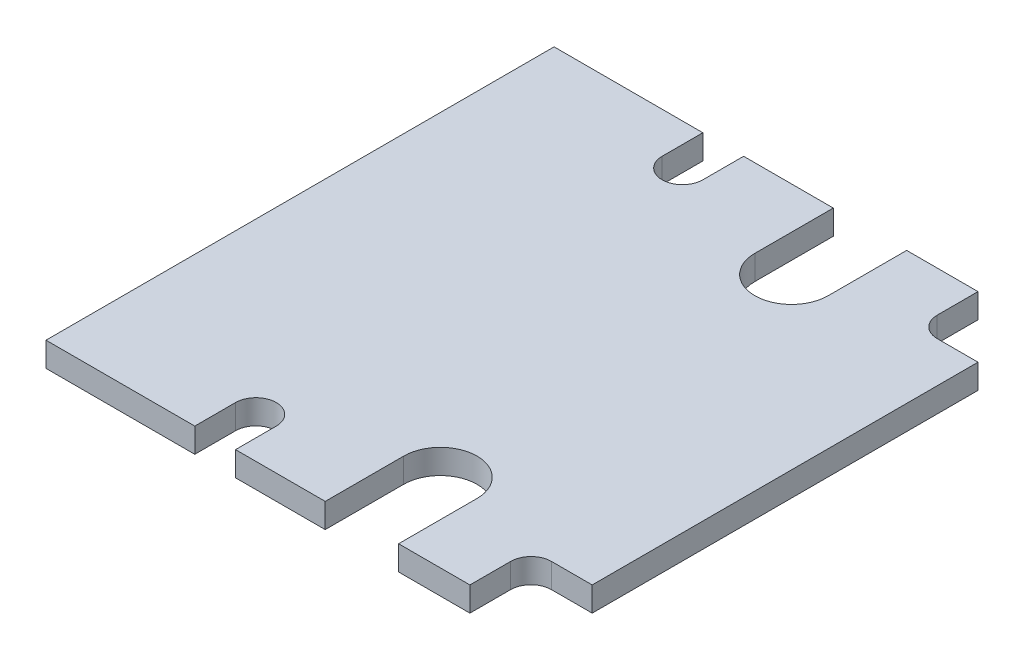
SolidWorks part; units mm, degrees
ref_plane "Front Plane" through (0, 0, 0) normal (0, 0, 1) x (1, 0, 0)
ref_plane "Top Plane" through (0, 0, 0) normal (0, 1, 0) x (1, 0, 0)
ref_plane "Right Plane" through (0, 0, 0) normal (1, 0, 0) x (0, 0, -1)
sketch "Sketch1" plane through (0, 0, 0) normal (0, 1, 0) x (1, 0, 0)
  line L0 (3.748, 8.0255) -> (5.748, 8.0255)
  line L1 (-18.052, 11.0255) -> (-10.752, 11.0255)
  line L2 (-18.052, 11.0255) -> (-18.052, -13.9045)
  line L3 (-18.052, -13.9045) -> (-10.752, -13.9045)
  line L4 (5.748, 8.0255) -> (5.748, -10.9045)
  line L5 (3.748, -10.9045) -> (5.748, -10.9045)
  line L6 (2.748, -11.9045) -> (2.748, -13.9045)
  line L7 (-10.752, -11.9045) -> (-10.752, -13.9045)
  line L8 (2.748, 9.0255) -> (2.748, 11.0255)
  line L9 (-8.752, -11.9045) -> (-8.752, -13.9045)
  line L10 (-8.752, -13.9045) -> (2.748, -13.9045)
  line L11 (-10.752, 9.0255) -> (-10.752, 11.0255)
  line L12 (-8.752, 9.0255) -> (-8.752, 11.0255)
  line L13 (-8.752, 11.0255) -> (2.748, 11.0255)
  arc A0 (2.748, 9.0255) -> (3.748, 8.0255) centre (3.748, 9.0255) ccw
  arc A1 (-10.752, 9.0255) -> (-8.752, 9.0255) centre (-9.752, 9.0255) ccw
  arc A2 (-8.752, -11.9045) -> (-10.752, -11.9045) centre (-9.752, -11.9045) ccw
  arc A3 (3.748, -10.9045) -> (2.748, -11.9045) centre (3.748, -11.9045) ccw
  dimension "D3" = 2
  dimension "D4" = 2
  dimension "D5" = 2
  dimension "D6" = 2
  dimension "D7" = 8.3
  dimension "D8" = 2
  dimension "D9" = 8.3
  dimension "D10" = 2
  dimension "D11" = 2
  dimension "D12" = 2
  dimension "D13" = 2
  dimension "D14" = 2
  dimension "D2" = 24.93
extrude "Boss-Extrude1" add sketch "Sketch1" along normal blind 1.2
sketch "Sketch2" plane through (0, 1.2, 0) normal (0, 1, 0) x (1, 0, 0)
  line L0 (-10.752, 11.0255) -> (-18.052, 11.0255) construction
  line L1 (5.748, -10.9045) -> (5.748, 8.0255) construction
  line L2 (-4.352, 7.1755) -> (-4.352, 11.0255)
  line L3 (-0.752, 7.1755) -> (-0.752, 11.0255)
  line L4 (-4.352, 11.0255) -> (-0.752, 11.0255)
  arc A0 (-4.352, 7.1755) -> (-0.752, 7.1755) centre (-2.552, 7.1755) ccw
  dimension "D1" = 3.85
  dimension "D2" = 3.6
  dimension "D3" = 8.3
extrude "Cut-Extrude2" cut sketch "Sketch2" against normal through all
ref_plane "Plane1" through (0, 0, 1.4395) normal (0, 0, 1) x (1, 0, 0)
mirror "Mirror2" about plane through (0, 0, 1.4395) normal (0, 0, 1) of "Cut-Extrude2"
